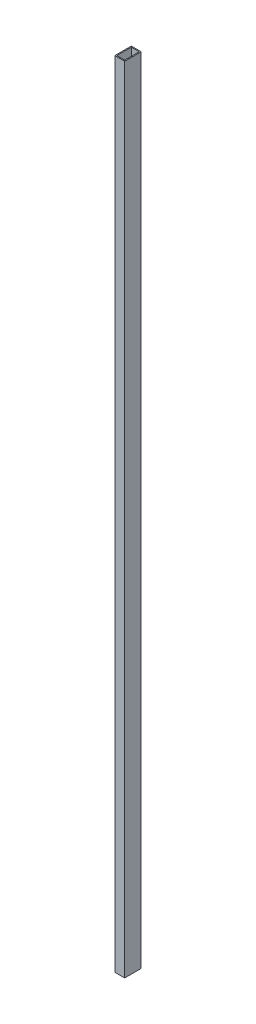
SolidWorks part; units mm, degrees
ref_plane "Front Plane" through (0, 0, 0) normal (0, 0, 1) x (1, 0, 0)
ref_plane "Top Plane" through (0, 0, 0) normal (0, 1, 0) x (1, 0, 0)
ref_plane "Right Plane" through (0, 0, 0) normal (1, 0, 0) x (0, 0, -1)
sketch "Sketch1" plane through (0, 0, 0) normal (0, 1, 0) x (1, 0, 0)
  line L0 (7.62, 7.62) -> (68.58, 7.62)
  line L1 (0, 0) -> (76.2, 0)
  line L2 (0, 0) -> (0, 127)
  line L3 (0, 127) -> (76.2, 127)
  line L4 (76.2, 0) -> (76.2, 127)
  line L5 (68.58, 7.62) -> (68.58, 119.38)
  line L6 (7.62, 119.38) -> (68.58, 119.38)
  line L7 (7.62, 7.62) -> (7.62, 119.38)
  dimension "D1" = 76.2
  dimension "D2" = 127
  dimension "D3" = 7.62
extrude "Boss-Extrude1" add sketch "Sketch1" along normal blind 6096
